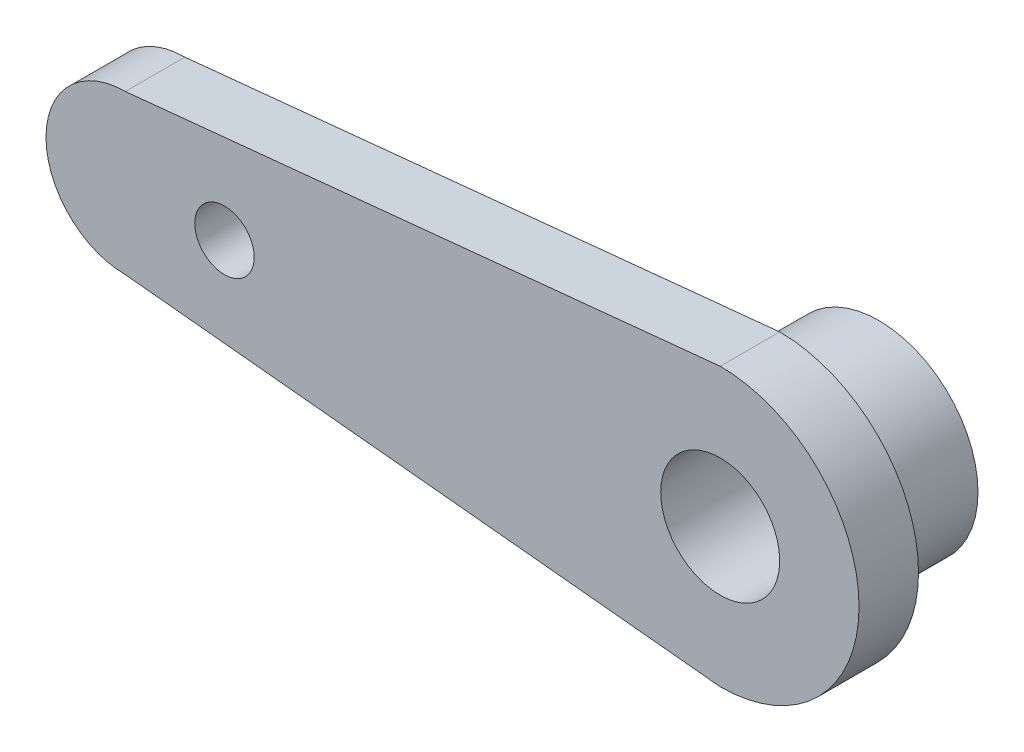
SolidWorks part; units mm, degrees
ref_plane "Front Plane" through (0, 0, 0) normal (0, 0, 1) x (1, 0, 0)
ref_plane "Top Plane" through (0, 0, 0) normal (0, 1, 0) x (1, 0, 0)
ref_plane "Right Plane" through (0, 0, 0) normal (1, 0, 0) x (0, 0, -1)
sketch "Sketch1" plane through (0, 0, 0) normal (0, 0, 1) x (1, 0, 0)
  circle A0 centre (0, 0) radius 3
  circle A1 centre (0, 0) radius 5
  dimension "D1" = 6
  dimension "D2" = 10
extrude "Boss-Extrude1" add sketch "Sketch1" along normal blind 5
sketch "Sketch2" plane through (0, 0, 5) normal (0, 0, 1) x (1, 0, 0)
  line L0 (-30, 4) -> (0, 7)
  line L1 (-30, -4) -> (0, -7)
  arc A0 (0, -7) -> (0, 7) centre (0, 0) ccw
  arc A1 (-30, 4) -> (-30, -4) centre (-30, 0) ccw
  dimension "D1" = 14
  dimension "D2" = 8
  dimension "D3" = 30
extrude "Boss-Extrude2" add sketch "Sketch2" along normal blind 3
sketch "Sketch3" plane through (0, 0, 5) normal (0, 0, -1) x (-1, 0, 0)
  circle A0 centre (25, 0) radius 1.5
  dimension "D1" = 3
  dimension "D2" = 25
extrude "Cut-Extrude1" cut sketch "Sketch3" against normal blind 3
sketch "Sketch4" plane through (0, 0, 5) normal (0, 0, -1) x (-1, 0, 0)
  circle A1 centre (0, 0) radius 3
  circle A2 centre (0, 0) radius 3
  dimension "D1" = 0
extrude "Cut-Extrude2" cut sketch "Sketch4" against normal blind 3
